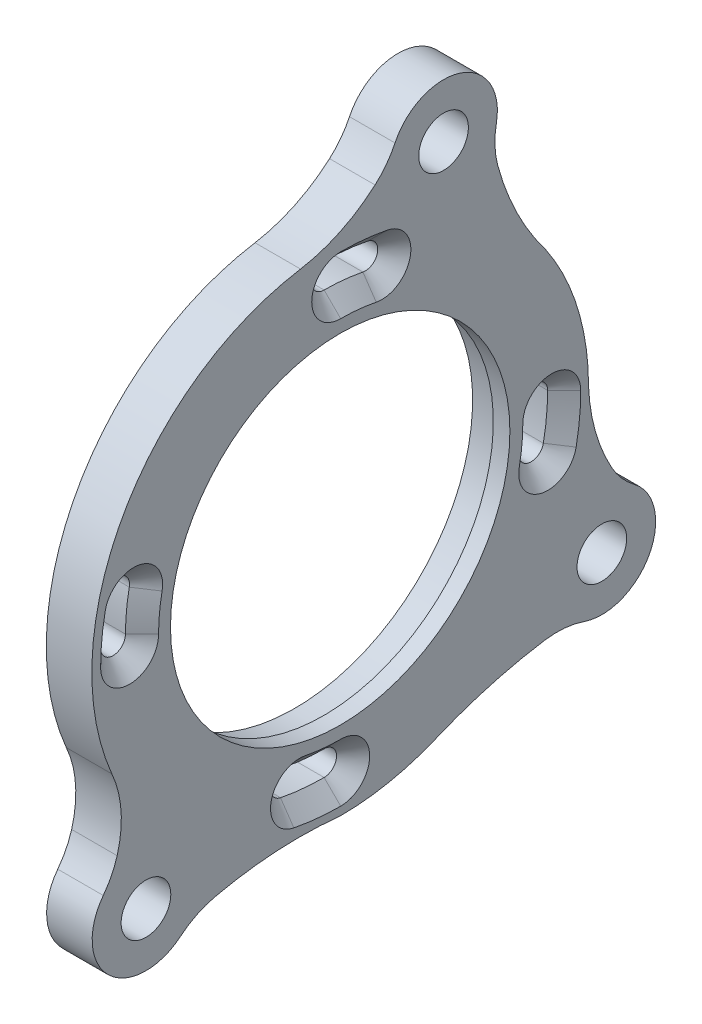
SolidWorks part; units mm, degrees
material "6063-T6"
ref_plane "Plan de face" through (0, 0, 0) normal (0, 0, 1) x (1, 0, 0)
ref_plane "Plan de dessus" through (0, 0, 0) normal (0, 1, 0) x (1, 0, 0)
ref_plane "Plan de droite" through (0, 0, 0) normal (1, 0, 0) x (0, 0, -1)
sketch "Esquisse1" plane through (0, 0, 0) normal (1, 0, 0) x (0, 0, -1)
  circle A0 centre (0, 0) radius 21.5
  circle A1 centre (0, 0) radius 20.5
  dimension "D1" = 43
  dimension "D2" = 41
extrude "Boss.-Extru.1" add sketch "Esquisse1" along normal blind 107
sketch "Esquisse2" plane through (107, 0, 0) normal (1, 0, 0) x (0, 0, -1)
  line L0 (0, 0) -> (-82.2923, 0) construction
  line L1 (0, 0) -> (-23.4617, -27.9606) construction
  circle A0 centre (0, 0) radius 20.5
  circle A1 centre (0, 0) radius 36.5 construction
  circle A2 centre (-23.4617, -27.9606) radius 3
  circle A3 centre (31.609, -18.2517) radius 3
  circle A4 centre (12.4874, 34.2975) radius 3
  circle A5 centre (0, 0) radius 30 construction
  circle A6 centre (-23.4617, -27.9606) radius 6.5 construction
  circle A7 centre (31.609, -18.2517) radius 6.5 construction
  circle A8 centre (12.4874, 34.2975) radius 6.5 construction
  arc A9 (6.2059, 35.9686) -> (18.3729, 31.5387) centre (12.4874, 34.2975) cw
  arc A10 (34.3451, -12.3556) -> (27.8704, -23.5689) centre (31.609, -18.2517) cw
  arc A11 (-28.0492, -23.3557) -> (-18.1302, -31.6788) centre (-23.4617, -27.9606) ccw
  arc A12 (-18.1302, -31.6788) -> (0, -30) centre (-4.8864, -75.9681) cw
  arc A13 (27.8704, -23.5689) -> (11.5312, -27.6953) centre (33.2979, -79.4718) ccw
  arc A14 (34.3451, -12.3556) -> (30, 0) centre (52.2811, 0.8938) cw
  arc A15 (6.2059, 35.9686) -> (-4.7864, 29.6157) centre (-7.8433, 47.5913) cw
  arc A16 (18.3729, 31.5387) -> (24.7711, 16.9231) centre (51.3807, 37.2802) ccw
  arc A17 (-4.7864, 29.6157) -> (-27.5823, -11.799) centre (0, 0) ccw
  arc A18 (-27.5823, -11.799) -> (-28.0492, -23.3557) centre (-39.3327, -17.1121) cw
  arc A19 (0, -30) -> (11.5312, -27.6953) centre (0, 0) ccw
  arc A20 (24.7711, 16.9231) -> (30, 0) centre (0, 0) cw
  circle A21 centre (-25.4391, 0) radius 1.5 construction
  circle A22 centre (0.0609, 0) radius 25.5 construction
  circle A23 centre (0.0609, 0) radius 25.5 construction
  circle A24 centre (0.0609, 25.5) radius 1.5 construction
  circle A25 centre (0.0609, 0) radius 25.5 construction
  circle A26 centre (25.5609, 0) radius 1.5 construction
  circle A27 centre (0.0609, 0) radius 25.5 construction
  circle A28 centre (0.0609, -25.5) radius 1.5 construction
  arc A29 (-25.4391, 0) -> (-24.9489, 4.9759) centre (0.0609, 0) cw construction
  arc A30 (-26.4201, 5.2686) -> (-26.9391, 0) centre (0.0609, 0) ccw
  arc A31 (-23.4778, 4.6832) -> (-23.9391, 0) centre (0.0609, 0) ccw
  arc A32 (-23.4778, 4.6832) -> (-26.4201, 5.2686) centre (-24.9489, 4.9759) ccw
  arc A33 (-26.9391, 0) -> (-23.9391, 0) centre (-25.4391, 0) ccw
  arc A34 (0.0609, 25.5) -> (5.0368, 25.0098) centre (0.0609, 0) cw construction
  arc A35 (5.3295, 26.481) -> (0.0609, 27) centre (0.0609, 0) ccw
  arc A36 (4.7441, 23.5386) -> (0.0609, 24) centre (0.0609, 0) ccw
  arc A37 (4.7441, 23.5386) -> (5.3295, 26.481) centre (5.0368, 25.0098) ccw
  arc A38 (0.0609, 27) -> (0.0609, 24) centre (0.0609, 25.5) ccw
  arc A39 (25.5609, 0) -> (25.0707, -4.9759) centre (0.0609, 0) cw construction
  arc A40 (26.5419, -5.2686) -> (27.0609, 0) centre (0.0609, 0) ccw
  arc A41 (23.5995, -4.6832) -> (24.0609, 0) centre (0.0609, 0) ccw
  arc A42 (23.5995, -4.6832) -> (26.5419, -5.2686) centre (25.0707, -4.9759) ccw
  arc A43 (27.0609, 0) -> (24.0609, 0) centre (25.5609, 0) ccw
  arc A44 (0.0609, -25.5) -> (-4.915, -25.0098) centre (0.0609, 0) cw construction
  arc A45 (-5.2077, -26.481) -> (0.0609, -27) centre (0.0609, 0) ccw
  arc A46 (-4.6223, -23.5386) -> (0.0609, -24) centre (0.0609, 0) ccw
  arc A47 (-4.6223, -23.5386) -> (-5.2077, -26.481) centre (-4.915, -25.0098) ccw
  arc A48 (0.0609, -27) -> (0.0609, -24) centre (0.0609, -25.5) ccw
  point P54 (0.0609, 0)
  point P55 (-25.3163, 2.5)
  point P65 (2.5609, 25.3772)
  point P72 (25.438, -2.5)
  point P79 (-2.4391, -25.3772)
  point P84 (0.0609, 0)
  dimension "D1" = 41
  dimension "D2" = 73
  dimension "D3" = 55.92
  dimension "D6" = 6
  dimension "D7" = 6
  dimension "D8" = 6
  dimension "D9" = 60
  dimension "D10" = 51
  dimension "D11" = 3
  dimension "D4" = 55.92
  dimension "D5" = 50
  dimension "D14" = 5
  dimension "D12" = 4
  dimension "D13" = 4
extrude "Boss.-Extru.2" add sketch "Esquisse2" against normal blind 5.5
sketch "Esquisse3" plane through (101.5, 0, 0) normal (-1, 0, 0) x (0, 0, 1)
  circle A0 centre (0, 0) radius 21.5
  circle A1 centre (0, 0) radius 21.55
  dimension "D1" = 43
  dimension "D2" = 43.1
chamfer "Chanfrein1" distance 2 angle 45 16 edges at (107, -2.6471, -26.9308) (107, 1.5, -25.5609) (107, -6.4471, -24.778) (107, -2.3529, -23.9453) (107, -26.8699, 2.5862) (107, -25.5, -1.5609) (107, -24.7171, 6.3862) (107, -23.8844, 2.2921) (107, 2.6471, 26.809) (107, -1.5, 25.4391) (107, 6.4471, 24.6562) (107, 2.3529, 23.8235) (107, 26.8699, -2.7079) (107, 25.5, 1.4391) (107, 24.7171, -6.508) (107, 23.8844, -2.4138)
fillet "Congé1" radius 10 6 edges at (104.25, -31.6788, 18.1302) (104.25, -23.3557, 28.0492) (104.25, 35.9686, -6.2059) (104.25, 31.5387, -18.3729) (104.25, -12.3556, -34.3451) (104.25, -23.5689, -27.8704)
sketch "Esquisse4" plane through (0, 0, 0) normal (-1, 0, 0) x (0, 0, 1)
  circle A0 centre (0, 0) radius 21.5
  circle A1 centre (0, 0) radius 20.5
extrude "Enlèv. mat.-Extru.2" cut sketch "Esquisse4" against normal blind 105
